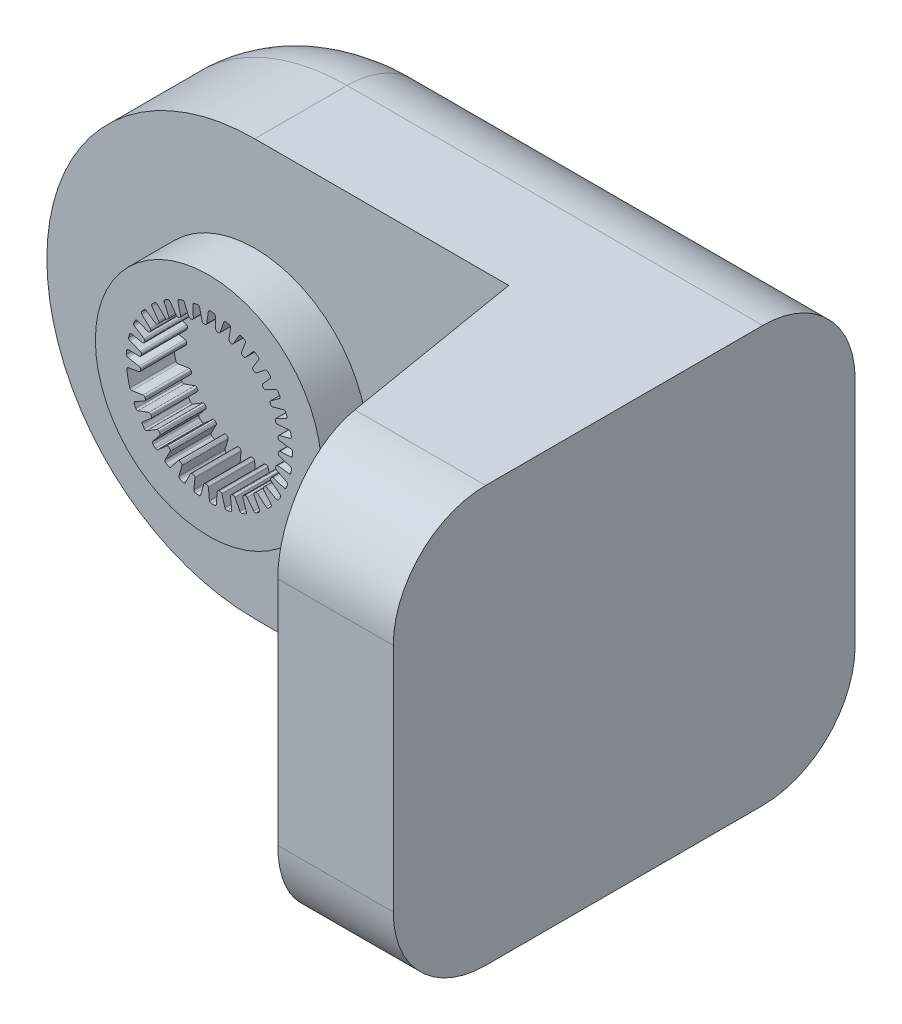
SolidWorks part; units mm, degrees
ref_plane "Front Plane" through (0, 0, 0) normal (0, 0, 1) x (1, 0, 0)
ref_plane "Top Plane" through (0, 0, 0) normal (0, 1, 0) x (1, 0, 0)
ref_plane "Right Plane" through (0, 0, 0) normal (1, 0, 0) x (0, 0, -1)
sketch "Sketch1" plane through (0, 0, 0) normal (0, 0, 1) x (1, 0, 0)
  line L0 (55, 0) -> (-55, 0) construction
  line L1 (-16.9691, -5.4979) -> (-14.565, -5.1246)
  line L2 (-14.1254, -5.3896) -> (-14.0498, -5.609)
  line L3 (-14.2318, -6.0878) -> (-16.2781, -7.2403)
  line L4 (-15.6283, -8.6059) -> (-13.3395, -7.7807)
  line L5 (-12.8575, -7.957) -> (-12.7414, -8.158)
  line L6 (-12.8287, -8.6627) -> (-14.6175, -10.1845)
  line L7 (-13.7191, -11.401) -> (-11.6298, -10.1543)
  line L8 (-11.1229, -10.2354) -> (-10.9707, -10.4105)
  line L9 (-10.96, -10.9225) -> (-12.4256, -12.7577)
  line L10 (-11.3116, -13.7804) -> (-9.4986, -12.158)
  line L11 (-8.9856, -12.1408) -> (-8.8027, -12.2837)
  line L12 (-8.6945, -12.7843) -> (-9.783, -14.8654)
  line L13 (-8.4943, -15.6568) -> (-7.0242, -13.7182)
  line L14 (-6.5239, -13.6035) -> (-6.3171, -13.7088)
  line L15 (-6.1154, -14.1796) -> (-6.7868, -16.4302)
  line L16 (-5.3708, -16.9611) -> (-4.2976, -14.7776)
  line L17 (-3.8283, -14.5696) -> (-3.6053, -14.6335)
  line L18 (-3.3174, -15.0571) -> (-3.5471, -17.3945)
  line L19 (-2.0557, -17.6455) -> (-1.4189, -15.2973)
  line L20 (-0.998, -15.0035) -> (-0.7668, -15.0238)
  line L21 (-0.4034, -15.3847) -> (-0.1828, -17.7229)
  line L22 (1.329, -17.6847) -> (1.5061, -15.2582)
  line L23 (1.8632, -14.8895) -> (2.094, -14.8652)
  line L24 (2.5196, -15.1502) -> (3.1822, -17.4034)
  line L25 (4.659, -17.0774) -> (4.3698, -14.6617)
  line L26 (4.65, -14.2316) -> (4.872, -14.1637)
  line L27 (5.3441, -14.3623) -> (6.4245, -16.4476)
  line L28 (7.8119, -15.8458) -> (7.0671, -13.5297)
  line L29 (7.2601, -13.054) -> (7.465, -12.9451)
  line L30 (7.9664, -13.0499) -> (9.4248, -14.8908)
  line L31 (10.6719, -14.0353) -> (9.4989, -11.9038)
  line L32 (9.5976, -11.4001) -> (9.7779, -11.254)
  line L33 (10.29, -11.2612) -> (12.073, -12.79)
  line L34 (13.1339, -11.7123) -> (11.5757, -9.8438)
  line L35 (11.5765, -9.3305) -> (11.7257, -9.1527)
  line L36 (12.2298, -9.0621) -> (14.2716, -10.2226)
  line L37 (15.1075, -8.9622) -> (13.2214, -7.4254)
  line L38 (13.1242, -6.9214) -> (13.2367, -6.7184)
  line L39 (13.7142, -6.5332) -> (15.94, -7.2828)
  line L40 (16.52, -5.8861) -> (14.3753, -4.7374)
  line L41 (14.1837, -4.2612) -> (14.2555, -4.0405)
  line L42 (14.6889, -3.7676) -> (17.0168, -4.0787)
  line L43 (17.3196, -2.597) -> (14.9951, -1.8786)
  line L44 (14.7162, -1.4477) -> (14.7445, -1.2173)
  line L45 (15.1179, -0.8668) -> (17.4624, -0.728)
  line L46 (17.477, 0.7843) -> (15.0581, 1.0459)
  line L47 (14.7021, 1.4157) -> (14.6859, 1.6472)
  line L48 (14.9856, 2.0626) -> (17.2605, 2.6462)
  line L49 (16.9862, 4.1334) -> (14.5619, 3.9288)
  line L50 (14.1419, 4.2238) -> (14.0818, 4.448)
  line L51 (14.2967, 4.9129) -> (16.4185, 5.9199)
  line L52 (15.8655, 7.3274) -> (13.5247, 6.6639)
  line L53 (13.0561, 6.8734) -> (12.9544, 7.082)
  line L54 (13.0766, 7.5794) -> (14.9673, 8.9727)
  line L55 (14.1559, 10.2489) -> (11.9847, 9.151)
  line L56 (11.4848, 9.2672) -> (11.3451, 9.4525)
  line L57 (11.3702, 9.9641) -> (12.9602, 11.6926)
  line L58 (11.9202, 12.7905) -> (9.9985, 11.2984)
  line L59 (9.4855, 11.3171) -> (9.3131, 11.4724)
  line L60 (9.2401, 11.9793) -> (10.4711, 13.9795)
  line L61 (9.2407, 14.8588) -> (7.6389, 13.0275)
  line L62 (7.1318, 12.9479) -> (6.9329, 13.0675)
  line L63 (6.7645, 13.5511) -> (7.5913, 15.7494)
  line L64 (6.2158, 16.3778) -> (4.9929, 14.2745)
  line L65 (4.5102, 14.0997) -> (4.2922, 14.1791)
  line L66 (4.0346, 14.6217) -> (4.4267, 16.9374)
  line L67 (2.9565, 17.2917) -> (2.1574, 14.9937)
  line L68 (1.7171, 14.73) -> (1.4878, 14.7663)
  line L69 (1.1505, 15.1517) -> (1.0936, 17.4997)
  line L70 (-0.4172, 17.567) -> (-0.7631, 15.1587)
  line L71 (-1.1451, 14.8159) -> (-1.377, 14.8078)
  line L72 (-1.7817, 15.1217) -> (-2.2855, 17.4156)
  line L73 (-3.7814, 17.1934) -> (-3.6615, 14.7634)
  line L74 (-3.971, 14.354) -> (-4.1972, 14.3018)
  line L75 (-4.6543, 14.5327) -> (-5.5866, 16.6884)
  line L76 (-7.0126, 16.1848) -> (-6.4312, 13.8224)
  line L77 (-6.6569, 13.3614) -> (-6.8689, 13.267)
  line L78 (-7.3617, 13.4065) -> (-8.6882, 15.3446)
  line L79 (-9.992, 14.5782) -> (-8.9705, 12.3701)
  line L80 (-9.1041, 11.8745) -> (-9.2942, 11.7414)
  line L81 (-9.8045, 11.7843) -> (-11.4765, 13.4337)
  line L82 (-12.61, 12.4326) -> (-11.1859, 10.46)
  line L83 (-11.2225, 9.948) -> (-11.3837, 9.7811)
  line L84 (-11.8929, 9.7258) -> (-13.8489, 11.0259)
  line L85 (-14.7706, 9.8269) -> (-12.9963, 8.1622)
  line L86 (-12.9345, 7.6527) -> (-13.0609, 7.458)
  line L87 (-13.5501, 7.3066) -> (-15.7182, 8.2096)
  line L88 (-16.3942, 6.8568) -> (-14.3349, 5.5613)
  line L89 (-14.177, 5.0729) -> (-14.264, 4.8577)
  line L90 (-14.7153, 4.6157) -> (-17.0159, 5.0884)
  line L91 (-17.4214, 3.6315) -> (-15.1526, 2.7527)
  line L92 (-14.9045, 2.3034) -> (-14.9488, 2.0756)
  line L93 (-15.3457, 1.7519) -> (-17.6942, 1.777)
  line L94 (-17.8142, 0.2694) -> (-15.4195, -0.1603)
  line L95 (-15.0901, -0.554) -> (-15.0901, -0.7861)
  line L96 (-15.418, -1.1795) -> (-17.7281, -1.6031)
  circle A0 centre (-0.372, 0) radius 24.5
  arc A1 (-18.0536, -2.0399) -> (-17.4139, -5.2165) centre (-0.1596, -0.0893) ccw
  arc A2 (-17.4139, -5.2165) -> (-16.9691, -5.4979) centre (-17.0305, -5.1026) ccw
  arc A3 (-14.1254, -5.3896) -> (-14.565, -5.1246) centre (-14.5036, -5.5198) ccw
  arc A4 (-14.2318, -6.0878) -> (-14.0498, -5.609) centre (-14.4281, -5.7393) ccw
  arc A5 (-16.2781, -7.2403) -> (-16.4437, -7.7593) centre (-16.0818, -7.5889) ccw
  arc A6 (-16.4437, -7.7593) -> (-16.1186, -8.4146) centre (-0.1596, -0.0893) ccw
  arc A7 (-16.1186, -8.4146) -> (-15.6283, -8.6059) centre (-15.764, -8.2296) ccw
  arc A8 (-12.8575, -7.957) -> (-13.3395, -7.7807) centre (-13.2039, -8.157) ccw
  arc A9 (-12.8287, -8.6627) -> (-12.7414, -8.158) centre (-13.0878, -8.358) ccw
  arc A10 (-14.6175, -10.1845) -> (-14.681, -10.7255) centre (-14.3583, -10.4892) ccw
  arc A11 (-14.681, -10.7255) -> (-14.2369, -11.3068) centre (-0.1596, -0.0893) ccw
  arc A12 (-14.2369, -11.3068) -> (-13.7191, -11.401) centre (-13.924, -11.0575) ccw
  arc A13 (-11.1229, -10.2354) -> (-11.6298, -10.1543) centre (-11.4248, -10.4978) ccw
  arc A14 (-10.96, -10.9225) -> (-10.9707, -10.4105) centre (-11.2726, -10.6729) ccw
  arc A15 (-12.4256, -12.7577) -> (-12.3847, -13.3009) centre (-12.1131, -13.0073) ccw
  arc A16 (-12.3847, -13.3009) -> (-11.8378, -13.7868) centre (-0.1596, -0.0893) ccw
  arc A17 (-11.8378, -13.7868) -> (-11.3116, -13.7804) centre (-11.5783, -13.4824) ccw
  arc A18 (-8.9856, -12.1408) -> (-9.4986, -12.158) centre (-9.2318, -12.456) ccw
  arc A19 (-8.6945, -12.7843) -> (-8.8027, -12.2837) centre (-9.049, -12.5989) ccw
  arc A20 (-9.783, -14.8654) -> (-9.6392, -15.3909) centre (-9.4286, -15.0508) ccw
  arc A21 (-9.6392, -15.3909) -> (-9.0097, -15.7634) centre (-0.1596, -0.0893) ccw
  arc A22 (-9.0097, -15.7634) -> (-8.4943, -15.6568) centre (-8.813, -15.4151) ccw
  arc A23 (-6.5239, -13.6035) -> (-7.0242, -13.7182) centre (-6.7055, -13.9599) ccw
  arc A24 (-6.1154, -14.1796) -> (-6.3171, -13.7088) centre (-6.4987, -14.0653) ccw
  arc A25 (-6.7868, -16.4302) -> (-6.5454, -16.9185) centre (-6.4035, -16.5446) ccw
  arc A26 (-6.5454, -16.9185) -> (-5.8563, -17.1641) centre (-0.1596, -0.0893) ccw
  arc A27 (-5.8563, -17.1641) -> (-5.3708, -16.9611) centre (-5.7297, -16.7847) ccw
  arc A28 (-3.8283, -14.5696) -> (-4.2976, -14.7776) centre (-3.9386, -14.9541) ccw
  arc A29 (-3.3174, -15.0571) -> (-3.6053, -14.6335) centre (-3.7155, -15.018) ccw
  arc A30 (-3.5471, -17.3945) -> (-3.2169, -17.8278) centre (-3.149, -17.4336) ccw
  arc A31 (-3.2169, -17.8278) -> (-2.4937, -17.9374) centre (-0.1596, -0.0893) ccw
  arc A32 (-2.4937, -17.9374) -> (-2.0557, -17.6455) centre (-2.4418, -17.5408) ccw
  arc A33 (-0.998, -15.0035) -> (-1.4189, -15.2973) centre (-1.0328, -15.402) ccw
  arc A34 (-0.4034, -15.3847) -> (-0.7668, -15.0238) centre (-0.8016, -15.4222) ccw
  arc A35 (-0.1828, -17.7229) -> (0.2239, -18.0853) centre (0.2154, -17.6853) ccw
  arc A36 (0.2239, -18.0853) -> (0.9548, -18.0548) centre (-0.1596, -0.0893) ccw
  arc A37 (0.9548, -18.0548) -> (1.329, -17.6847) centre (0.93, -17.6556) ccw
  arc A38 (1.8632, -14.8895) -> (1.5061, -15.2582) centre (1.905, -15.2873) ccw
  arc A39 (2.5196, -15.1502) -> (2.094, -14.8652) centre (2.1358, -15.263) ccw
  arc A40 (3.1822, -17.4034) -> (3.6506, -17.6814) centre (3.566, -17.2905) ccw
  arc A41 (3.6506, -17.6814) -> (4.3623, -17.5121) centre (-0.1596, -0.0893) ccw
  arc A42 (4.3623, -17.5121) -> (4.659, -17.0774) centre (4.2618, -17.1249) ccw
  arc A43 (4.65, -14.2316) -> (4.3698, -14.6617) centre (4.767, -14.6141) ccw
  arc A44 (5.3441, -14.3623) -> (4.872, -14.1637) centre (4.9889, -14.5463) ccw
  arc A45 (6.4245, -16.4476) -> (6.9374, -16.6312) centre (6.7797, -16.2636) ccw
  arc A46 (6.9374, -16.6312) -> (7.6036, -16.3292) centre (-0.1596, -0.0893) ccw
  arc A47 (7.6036, -16.3292) -> (7.8119, -15.8458) centre (7.4311, -15.9683) ccw
  arc A48 (7.2601, -13.054) -> (7.0671, -13.5297) centre (7.4479, -13.4072) ccw
  arc A49 (7.9664, -13.0499) -> (7.465, -12.9451) centre (7.6528, -13.2983) ccw
  arc A50 (9.4248, -14.8908) -> (9.9633, -14.9731) centre (9.7384, -14.6424) ccw
  arc A51 (9.9633, -14.9731) -> (10.5597, -14.5495) centre (-0.1596, -0.0893) ccw
  arc A52 (10.5597, -14.5495) -> (10.6719, -14.0353) centre (10.3215, -14.2282) ccw
  arc A53 (9.5976, -11.4001) -> (9.4989, -11.9038) centre (9.8493, -11.7109) ccw
  arc A54 (10.29, -11.2612) -> (9.7779, -11.254) centre (10.0297, -11.5649) ccw
  arc A55 (12.073, -12.79) -> (12.6173, -12.7681) centre (12.3334, -12.4864) ccw
  arc A56 (12.6173, -12.7681) -> (13.1219, -12.2385) centre (-0.1596, -0.0893) ccw
  arc A57 (13.1219, -12.2385) -> (13.1339, -11.7123) centre (12.8267, -11.9685) ccw
  arc A58 (11.5765, -9.3305) -> (11.5757, -9.8438) centre (11.8829, -9.5876) ccw
  arc A59 (12.2298, -9.0621) -> (11.7257, -9.1527) centre (12.0321, -9.4099) ccw
  arc A60 (14.2716, -10.2226) -> (14.8018, -10.0972) centre (14.4693, -9.8748) ccw
  arc A61 (14.8018, -10.0972) -> (15.196, -9.481) centre (-0.1596, -0.0893) ccw
  arc A62 (15.196, -9.481) -> (15.1075, -8.9622) centre (14.8548, -9.2723) ccw
  arc A63 (13.1242, -6.9214) -> (13.2214, -7.4254) centre (13.474, -7.1153) ccw
  arc A64 (13.7142, -6.5332) -> (13.2367, -6.7184) centre (13.5866, -6.9123) ccw
  arc A65 (15.94, -7.2828) -> (16.4365, -7.0586) centre (16.0677, -6.9037) ccw
  arc A66 (16.4365, -7.0586) -> (16.7059, -6.3785) centre (-0.1596, -0.0893) ccw
  arc A67 (16.7059, -6.3785) -> (16.52, -5.8861) centre (16.3311, -6.2387) ccw
  arc A68 (14.1837, -4.2612) -> (14.3753, -4.7374) centre (14.5642, -4.3848) ccw
  arc A69 (14.6889, -3.7676) -> (14.2555, -4.0405) centre (14.6359, -4.1641) ccw
  arc A70 (17.0168, -4.0787) -> (17.4613, -3.7638) centre (17.0698, -3.6822) ccw
  arc A71 (17.4613, -3.7638) -> (17.5961, -3.0448) centre (-0.1596, -0.0893) ccw
  arc A72 (17.5961, -3.0448) -> (17.3196, -2.597) centre (17.2015, -2.9792) ccw
  arc A73 (14.7162, -1.4477) -> (14.9951, -1.8786) centre (15.1133, -1.4964) ccw
  arc A74 (15.1179, -0.8668) -> (14.7445, -1.2173) centre (15.1415, -1.2661) ccw
  arc A75 (17.4624, -0.728) -> (17.8387, -0.3341) centre (17.4388, -0.3287) ccw
  arc A76 (17.8387, -0.3341) -> (17.8338, 0.3974) centre (-0.1596, -0.0893) ccw
  arc A77 (17.8338, 0.3974) -> (17.477, 0.7843) centre (17.434, 0.3866) ccw
  arc A78 (14.7021, 1.4157) -> (15.0581, 1.0459) centre (15.1011, 1.4436) ccw
  arc A79 (14.9856, 2.0626) -> (14.6859, 1.6472) centre (15.085, 1.6751) ccw
  arc A80 (17.2605, 2.6462) -> (17.5547, 3.1046) centre (17.1611, 3.0337) ccw
  arc A81 (17.5547, 3.1046) -> (17.4103, 3.8218) centre (-0.1596, -0.0893) ccw
  arc A82 (17.4103, 3.8218) -> (16.9862, 4.1334) centre (17.0199, 3.7348) ccw
  arc A83 (14.1419, 4.2238) -> (14.5619, 3.9288) centre (14.5283, 4.3274) ccw
  arc A84 (14.2967, 4.9129) -> (14.0818, 4.448) centre (14.4682, 4.5515) ccw
  arc A85 (16.4185, 5.9199) -> (16.6198, 6.426) centre (16.247, 6.2812) ccw
  arc A86 (16.6198, 6.426) -> (16.3413, 7.1024) centre (-0.1596, -0.0893) ccw
  arc A87 (16.3413, 7.1024) -> (15.8655, 7.3274) centre (15.9746, 6.9426) ccw
  arc A88 (13.0561, 6.8734) -> (13.5247, 6.6639) centre (13.4156, 7.0488) ccw
  arc A89 (13.0766, 7.5794) -> (12.9544, 7.082) centre (13.3139, 7.2574) ccw
  arc A90 (14.9673, 8.9727) -> (15.0684, 9.508) centre (14.73, 9.2947) ccw
  arc A91 (15.0684, 9.508) -> (14.6658, 10.1188) centre (-0.1596, -0.0893) ccw
  arc A92 (14.6658, 10.1188) -> (14.1559, 10.2489) centre (14.3364, 9.8919) ccw
  arc A93 (11.4848, 9.2672) -> (11.9847, 9.151) centre (11.8042, 9.5079) ccw
  arc A94 (11.3702, 9.9641) -> (11.3451, 9.4525) centre (11.6646, 9.6932) ccw
  arc A95 (12.9602, 11.6926) -> (12.9573, 12.2373) centre (12.6658, 11.9634) ccw
  arc A96 (12.9573, 12.2373) -> (12.4456, 12.7601) centre (-0.1596, -0.0893) ccw
  arc A97 (12.4456, 12.7601) -> (11.9202, 12.7905) centre (12.1655, 12.4745) ccw
  arc A98 (9.4855, 11.3171) -> (9.9985, 11.2984) centre (9.7532, 11.6144) ccw
  arc A99 (9.2401, 11.9793) -> (9.3131, 11.4724) centre (9.5807, 11.7697) ccw
  arc A100 (10.4711, 13.9795) -> (10.3643, 14.5136) centre (10.1304, 14.1891) ccw
  arc A101 (10.3643, 14.5136) -> (9.7623, 14.9292) centre (-0.1596, -0.0893) ccw
  arc A102 (9.7623, 14.9292) -> (9.2407, 14.8588) centre (9.5418, 14.5954) ccw
  arc A103 (7.1318, 12.9479) -> (7.6389, 13.0275) centre (7.3379, 13.2908) ccw
  arc A104 (6.7645, 13.5511) -> (6.9329, 13.0675) centre (7.1389, 13.4103) ccw
  arc A105 (7.5913, 15.7494) -> (7.3846, 16.2534) centre (7.2169, 15.8902) ccw
  arc A106 (7.3846, 16.2534) -> (6.7143, 16.5464) centre (-0.1596, -0.0893) ccw
  arc A107 (6.7143, 16.5464) -> (6.2158, 16.3778) centre (6.5616, 16.1768) ccw
  arc A108 (4.5102, 14.0997) -> (4.9929, 14.2745) centre (4.6471, 14.4756) ccw
  arc A109 (4.0346, 14.6217) -> (4.2922, 14.1791) centre (4.429, 14.5549) ccw
  arc A110 (4.4267, 16.9374) -> (4.1276, 17.3926) centre (4.0323, 17.0042) ccw
  arc A111 (4.1276, 17.3926) -> (3.4138, 17.5524) centre (-0.1596, -0.0893) ccw
  arc A112 (3.4138, 17.5524) -> (2.9565, 17.2917) centre (3.3343, 17.1604) ccw
  arc A113 (1.7171, 14.73) -> (2.1574, 14.9937) centre (1.7796, 15.1251) ccw
  arc A114 (1.1505, 15.1517) -> (1.4878, 14.7663) centre (1.5504, 15.1614) ccw
  arc A115 (1.0936, 17.4997) -> (0.7131, 17.8895) centre (0.6937, 17.49) ccw
  arc A116 (0.7131, 17.8895) -> (-0.0181, 17.9101) centre (-0.1596, -0.0893) ccw
  arc A117 (-0.0181, 17.9101) -> (-0.4172, 17.567) centre (-0.0212, 17.5101) ccw
  arc A118 (-1.1451, 14.8159) -> (-0.7631, 15.1587) centre (-1.1591, 15.2156) ccw
  arc A119 (-1.7817, 15.1217) -> (-1.377, 14.8078) centre (-1.391, 15.2075) ccw
  arc A120 (-2.2855, 17.4156) -> (-2.7334, 17.7257) centre (-2.6762, 17.3298) ccw
  arc A121 (-2.7334, 17.7257) -> (-3.4552, 17.6064) centre (-0.1596, -0.0893) ccw
  arc A122 (-3.4552, 17.6064) -> (-3.7814, 17.1934) centre (-3.3819, 17.2132) ccw
  arc A123 (-3.971, 14.354) -> (-3.6615, 14.7634) centre (-4.061, 14.7437) ccw
  arc A124 (-4.6543, 14.5327) -> (-4.1972, 14.3018) centre (-4.2871, 14.6915) ccw
  arc A125 (-5.5866, 16.6884) -> (-6.0854, 16.9073) centre (-5.9537, 16.5296) ccw
  arc A126 (-6.0854, 16.9073) -> (-6.7711, 16.6525) centre (-0.1596, -0.0893) ccw
  arc A127 (-6.7711, 16.6525) -> (-7.0126, 16.1848) centre (-6.6242, 16.2804) ccw
  arc A128 (-6.6569, 13.3614) -> (-6.4312, 13.8224) centre (-6.8196, 13.7268) ccw
  arc A129 (-7.3617, 13.4065) -> (-6.8689, 13.267) centre (-7.0316, 13.6324) ccw
  arc A130 (-8.6882, 15.3446) -> (-9.2196, 15.4643) centre (-9.0183, 15.1187) ccw
  arc A131 (-9.2196, 15.4643) -> (-9.8441, 15.0833) centre (-0.1596, -0.0893) ccw
  arc A132 (-9.8441, 15.0833) -> (-9.992, 14.5782) centre (-9.6289, 14.7462) ccw
  arc A133 (-9.1041, 11.8745) -> (-8.9705, 12.3701) centre (-9.3335, 12.2021) ccw
  arc A134 (-9.8045, 11.7843) -> (-9.2942, 11.7414) centre (-9.5236, 12.069) ccw
  arc A135 (-11.4765, 13.4337) -> (-12.021, 13.4498) centre (-11.7574, 13.1489) ccw
  arc A136 (-12.021, 13.4498) -> (-12.5613, 12.9567) centre (-0.1596, -0.0893) ccw
  arc A137 (-12.5613, 12.9567) -> (-12.61, 12.4326) centre (-12.2857, 12.6668) ccw
  arc A138 (-11.2225, 9.948) -> (-11.1859, 10.46) centre (-11.5103, 10.2259) ccw
  arc A139 (-11.8929, 9.7258) -> (-11.3837, 9.7811) centre (-11.6715, 10.0589) ccw
  arc A140 (-13.8489, 11.0259) -> (-14.3864, 10.9378) centre (-14.0703, 10.6928) ccw
  arc A141 (-14.3864, 10.9378) -> (-14.8227, 10.3506) centre (-0.1596, -0.0893) ccw
  arc A142 (-14.8227, 10.3506) -> (-14.7706, 9.8269) centre (-14.4969, 10.1186) ccw
  arc A143 (-12.9345, 7.6527) -> (-12.9963, 8.1622) centre (-13.27, 7.8705) ccw
  arc A144 (-13.5501, 7.3066) -> (-13.0609, 7.458) centre (-13.3963, 7.6759) ccw
  arc A145 (-15.7182, 8.2096) -> (-16.2291, 8.0206) centre (-15.872, 7.8404) ccw
  arc A146 (-16.2291, 8.0206) -> (-16.5454, 7.361) centre (-0.1596, -0.0893) ccw
  arc A147 (-16.5454, 7.361) -> (-16.3942, 6.8568) centre (-16.1812, 7.1954) ccw
  arc A148 (-14.177, 5.0729) -> (-14.3349, 5.5613) centre (-14.5479, 5.2227) ccw
  arc A149 (-14.7153, 4.6157) -> (-14.264, 4.8577) centre (-14.6348, 5.0075) ccw
  arc A150 (-17.0159, 5.0884) -> (-17.4813, 4.8054) centre (-17.0964, 4.6966) ccw
  arc A151 (-17.4813, 4.8054) -> (-17.6659, 4.0975) centre (-0.1596, -0.0893) ccw
  arc A152 (-17.6659, 4.0975) -> (-17.4214, 3.6315) centre (-17.2769, 4.0045) ccw
  arc A153 (-14.9045, 2.3034) -> (-15.1526, 2.7527) centre (-15.2971, 2.3797) ccw
  arc A154 (-15.3457, 1.7519) -> (-14.9488, 2.0756) centre (-15.3414, 2.1519) ccw
  arc A155 (-17.6942, 1.777) -> (-18.097, 1.4103) centre (-17.6984, 1.377) ccw
  arc A156 (-18.097, 1.4103) -> (-18.1432, 0.6803) centre (-0.1596, -0.0893) ccw
  arc A157 (-18.1432, 0.6803) -> (-17.8142, 0.2694) centre (-17.7435, 0.6632) ccw
  arc A158 (-15.0901, -0.554) -> (-15.4195, -0.1603) centre (-15.4901, -0.554) ccw
  arc A159 (-15.418, -1.1795) -> (-15.0901, -0.7861) centre (-15.4901, -0.7861) ccw
  arc A160 (-17.7281, -1.6031) -> (-18.0536, -2.0399) centre (-17.656, -1.9965) ccw
  dimension "D1" = 49
extrude "Boss-Extrude1" add sketch "Sketch1" along normal blind 10
sketch "Sketch6" plane through (0, 0, 0) normal (0, 0, 1) x (1, 0, 0)
  line L0 (-0.372, 0) -> (89.628, 0) construction
  line L1 (-0.372, 45) -> (89.628, 45)
  line L2 (89.628, -45) -> (-0.372, -45)
  line L3 (89.628, 45) -> (89.628, -45)
  arc A2 (-0.372, 45) -> (-0.372, -45) centre (-0.372, 0) ccw
  dimension "D1" = 90
extrude "Boss-Extrude3" add sketch "Sketch6" against normal blind 40
sketch "Sketch7" plane through (0, 0, 0) normal (0, 0, 1) x (1, 0, 0)
  line L0 (-0.372, -45) -> (89.628, -45) construction
  line L1 (89.628, 45) -> (54.628, 45)
  line L2 (89.628, 45) -> (89.628, -45)
  line L3 (89.628, -45) -> (54.628, -45)
  line L4 (54.628, 45) -> (54.628, -45)
  dimension "D1" = 35
extrude "Boss-Extrude4" add sketch "Sketch7" along normal blind 60
sketch "Sketch8" plane through (0, 45, 0) normal (0, 1, 0) x (1, 0, 0)
  line L0 (54.628, 0) -> (64.628, -60)
  line L1 (89.628, -60) -> (54.628, -60) construction
  line L2 (64.628, -60) -> (54.628, -60)
  line L3 (54.628, -60) -> (54.628, 0)
  dimension "D1" = 10
extrude "Cut-Extrude1" cut sketch "Sketch8" against normal through all
fillet "Fillet1" radius 20 3 edges at (44.628, -45, -40) (-45.372, 0, -40) (44.628, 45, -40)
fillet "Fillet2" radius 20 2 edges at (77.128, -45, 60) (77.128, 45, 60)
scale "Scale1" scale about centroid uniform scaling yes scale factor 0.3
